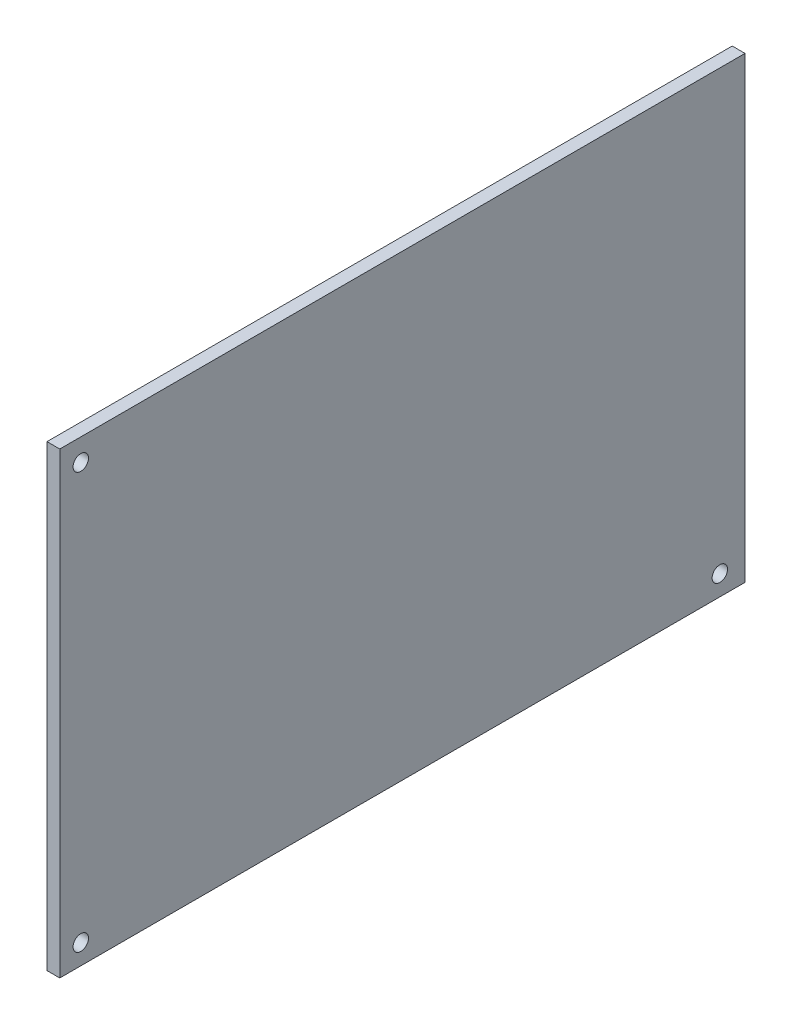
SolidWorks part; units mm, degrees
ref_plane "Plano frontal" through (0, 0, 0) normal (0, 0, 1) x (1, 0, 0)
ref_plane "Plano superior" through (0, 0, 0) normal (0, 1, 0) x (1, 0, 0)
ref_plane "Plano direito" through (0, 0, 0) normal (1, 0, 0) x (0, 0, -1)
sketch "Esboço1" plane through (0, 0, 0) normal (1, 0, 0) x (0, 0, -1)
  line L1 (0, 0) -> (89, 0)
  line L2 (0, 0) -> (0, 59.5)
  line L3 (0, 59.5) -> (89, 59.5)
  line L4 (89, 0) -> (89, 59.5)
  dimension "D1" = 59.5
  dimension "D2" = 89
extrude "Ressalto-extrusão1" add sketch "Esboço1" along normal blind 1.66
sketch "Esboço2" plane through (0, 0, 0) normal (-1, 0, 0) x (0, 0, 1)
  line L2 (-2.7319, 56.6237) -> (-2.7319, 0) construction
  line L5 (0, 0) -> (-89, 0) construction
  line L6 (0, 2.6237) -> (-89, 2.6237) construction
  line L7 (0, 59.5) -> (0, 0) construction
  line L8 (-89, 0) -> (-89, 59.5) construction
  circle A0 centre (-85.7319, 2.6237) radius 1
  circle A1 centre (-2.7319, 2.6237) radius 1
  circle A2 centre (-2.7319, 56.6237) radius 1
  dimension "D1" = 2
  dimension "D4" = 83
  dimension "D7" = 2
  dimension "D2" = 2
  dimension "D3" = 54
extrude "Corte-extrusão1" cut sketch "Esboço2" against normal through all
